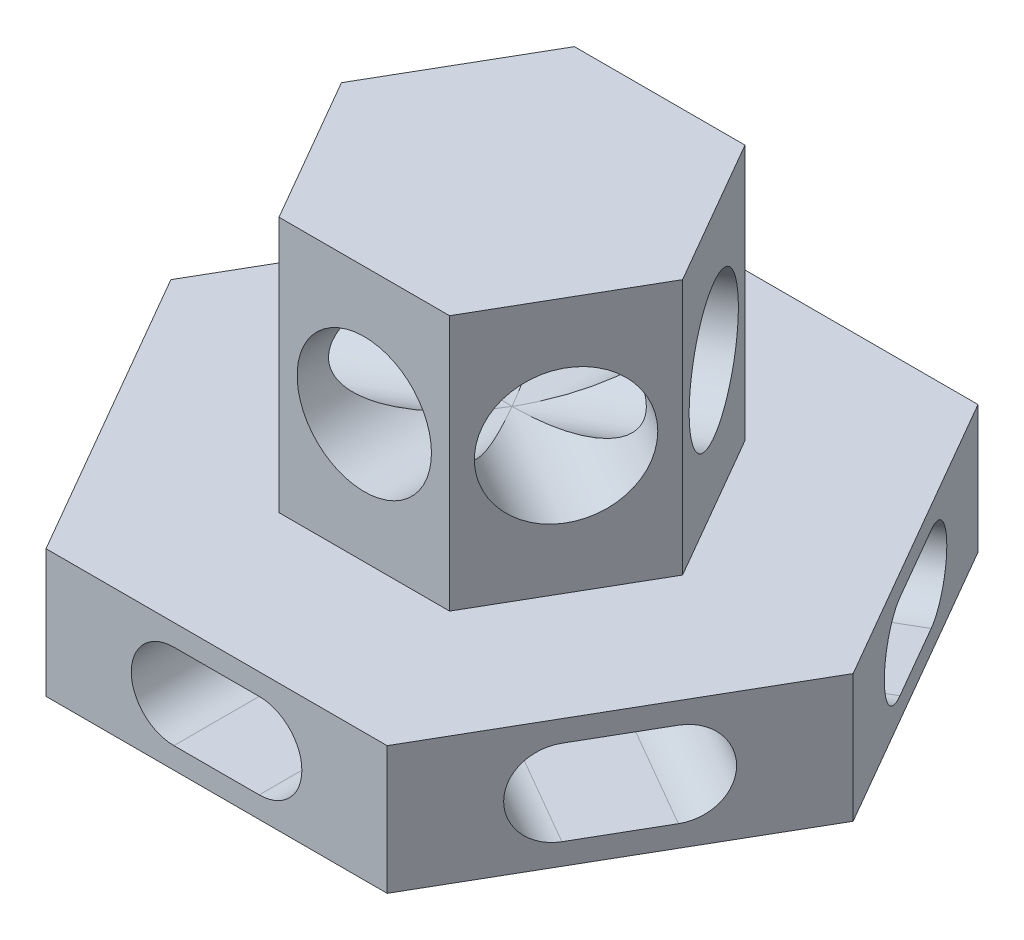
SolidWorks part; units mm, degrees
ref_plane "Alzado" through (0, 0, 0) normal (0, 0, 1) x (1, 0, 0)
ref_plane "Planta" through (0, 0, 0) normal (0, 1, 0) x (1, 0, 0)
ref_plane "Vista lateral" through (0, 0, 0) normal (1, 0, 0) x (0, 0, -1)
sketch "Croquis1" plane through (0, 0, 0) normal (0, 1, 0) x (1, 0, 0)
  line L1 (40, 69.282) -> (-40, 69.282)
  line L2 (-40, 69.282) -> (-80, 0)
  line L3 (-80, 0) -> (-40, -69.282)
  line L4 (-40, -69.282) -> (40, -69.282)
  line L5 (40, -69.282) -> (80, 0)
  line L6 (80, 0) -> (40, 69.282)
  circle A0 centre (0, 0) radius 69.282 construction
  dimension "D1" = 80
sketch "Croquis2" plane through (0, 0, 0) normal (0, 1, 0) x (1, 0, 0)
  line L7 (20, 34.641) -> (-20, 34.641)
  line L8 (-20, 34.641) -> (-40, 0)
  line L9 (-40, 0) -> (-20, -34.641)
  line L10 (-20, -34.641) -> (20, -34.641)
  line L11 (20, -34.641) -> (40, 0)
  line L12 (40, 0) -> (20, 34.641)
  circle A1 centre (0, 0) radius 34.641 construction
  dimension "D1" = 40
extrude "Saliente-Extruir1" add sketch "Croquis1" along normal blind 30
extrude "Saliente-Extruir2" add sketch "Croquis2" along normal blind 90
sketch "Croquis3" plane through (60, 0, 34.641) normal (0.866, 0, 0.5) x (0.5, 0, -0.866)
  line L0 (-10, 15) -> (10, 15) construction
  line L1 (-10, 25) -> (10, 25)
  line L2 (-10, 5) -> (10, 5)
  line L3 (-40, 0) -> (40, 0) construction
  arc A0 (-10, 25) -> (-10, 5) centre (-10, 15) ccw
  arc A1 (10, 5) -> (10, 25) centre (10, 15) ccw
  point P2 (0, 15)
  dimension "D1" = 10
  dimension "D2" = 20
  dimension "D3" = 5
extrude "Cortar-Extruir1" cut sketch "Croquis3" against normal up to next (138.5641 mm away)
pattern_circular "MatrizC1" count 6 over 360 about axis through (0, 0, 0) along (0, 1, 0) of "Cortar-Extruir1"
sketch "Croquis4" plane through (30, 0, -17.3205) normal (0.866, 0, -0.5) x (-0.5, 0, -0.866)
  line L0 (-40, 30) -> (40, 30) construction
  circle A0 centre (0, 60) radius 15.75
  dimension "D1" = 31.5
  dimension "D2" = 30
extrude "Cortar-Extruir2" cut sketch "Croquis4" against normal up to next (103.923 mm away)
pattern_circular "MatrizC2" count 6 over 360 about axis through (0, 90, 0) along (0, 1, 0) of "Cortar-Extruir2"
